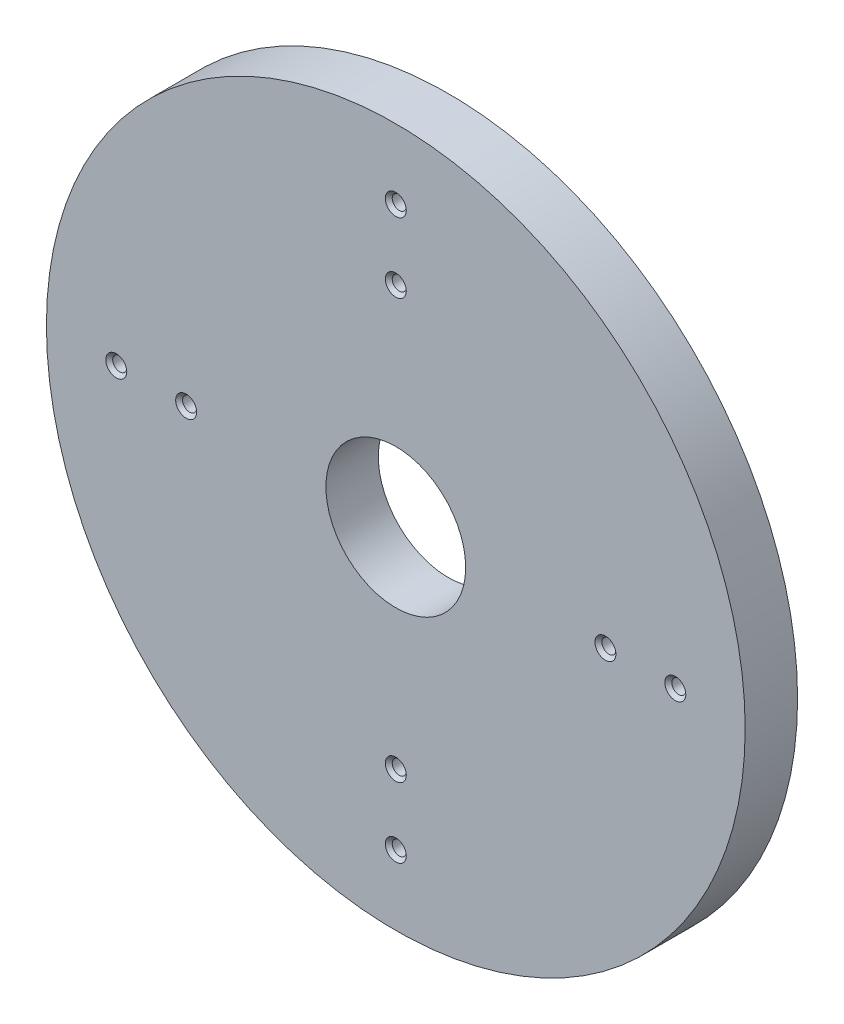
SolidWorks part; units mm, degrees
material "6061-T6 (SS)"
ref_plane "Front Plane" through (0, 0, 0) normal (0, 0, 1) x (1, 0, 0)
ref_plane "Top Plane" through (0, 0, 0) normal (0, 1, 0) x (1, 0, 0)
ref_plane "Right Plane" through (0, 0, 0) normal (1, 0, 0) x (0, 0, -1)
sketch "Sketch1" plane through (0, 0, 0) normal (0, 0, 1) x (1, 0, 0)
  line L1 (127, 127) -> (-127, 127)
  line L2 (127, 127) -> (127, -127)
  line L3 (127, -127) -> (-127, -127)
  line L4 (-127, 127) -> (-127, -127)
  line L5 (127, 127) -> (-127, -127) construction
  line L6 (127, -127) -> (-127, 127) construction
  line L7 (114.3, 114.3) -> (-114.3, 114.3) construction
  line L8 (114.3, 114.3) -> (114.3, -114.3) construction
  line L9 (114.3, -114.3) -> (-114.3, -114.3) construction
  line L10 (-114.3, 114.3) -> (-114.3, -114.3) construction
  line L11 (0, -114.3) -> (0, 114.3) construction
  line L12 (114.3, 0) -> (-114.3, 0) construction
  circle A0 centre (0, 0) radius 127
  circle A1 centre (0, 0) radius 25.4
  point P0 (0, 0)
  dimension "D3" = 50.8
  dimension "D1" = 254
  dimension "D2" = 228.6
extrude "Boss-Extrude2" add sketch "Sketch1" along normal blind 19.05 separate body contours A0
hole_wizard "1/4-20 Tapped Hole1" positions "Sketch4" profile "Sketch5" tap size "1/4-20" standard "ANSI Inch" end condition up to next
sketch "Sketch4" plane through (0, 0, 19.05) normal (0, 0, 1) x (1, 0, 0)
  line L0 (0, 0) -> (0, 101.6) construction
  point P2 (0, 101.6)
  point P8 (0, 76.2)
  point P18 (101.6, 0)
  point P19 (76.2, 0)
  point P20 (0, -101.6)
  point P21 (0, -76.2)
  point P22 (-101.6, 0)
  point P23 (-76.2, 0)
  dimension "D1" = 76.2
  dimension "D2" = 25.4
  dimension "D3" = 4
sketch "Sketch5" plane through (-76.2, 0, 19.05) normal (1, 0, 0) x (0, -1, 0)
  line L0 (0, 0) -> (0, 19.05)
  line L1 (0, 19.05) -> (3.81, 19.05)
  line L2 (2.5527, 17.7927) -> (2.5527, 1.2573)
  line L3 (2.5527, 1.2573) -> (3.81, 0)
  line L5 (3.81, 0) -> (0, 0)
  line L6 (-2.5527, 1.2573) -> (-3.81, 0) construction
  line L7 (3.81, 19.05) -> (2.5527, 17.7927)
  line L8 (-3.81, 19.05) -> (-2.5527, 17.7927) construction
  line L11 (0, -6.35) -> (0, 107.95) construction
  dimension "Thru Tap Drill Dia." = 5.1054
  dimension "Thru Tap Drill Depth" = 19.05
  dimension "Near C'Sink Dia." = 7.62
  dimension "Near C'Sink Angle" = 90
  dimension "Far C'Sink Dia." = 7.62
  dimension "Far C'Sink Angle" = 90
cosmetic thread "Hole Thread1" parameters "D2"=6.35
cosmetic thread "Hole Thread2" parameters "D2"=6.35
cosmetic thread "Hole Thread3" parameters "D2"=6.35
cosmetic thread "Hole Thread4" parameters "D2"=6.35
cosmetic thread "Hole Thread5" parameters "D2"=6.35
cosmetic thread "Hole Thread6" parameters "D2"=6.35
cosmetic thread "Hole Thread7" parameters "D2"=6.35
cosmetic thread "Hole Thread8" parameters "D2"=6.35
ref_plane "Plane1" through (0, 0, 0) normal (1, 0, 0) x (0, 1, 0)
ref_plane "Plane2" through (0, 0, 0) normal (0, 1, 0) x (-1, 0, 0)
